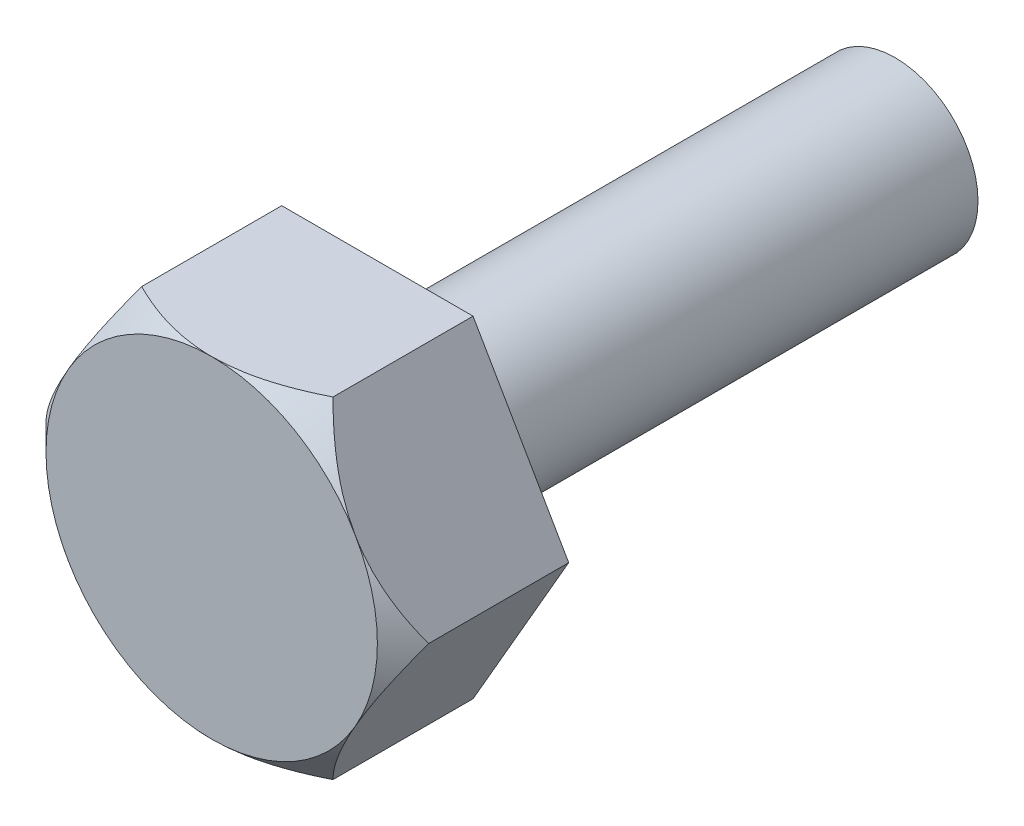
SolidWorks part; units mm, degrees
ref_plane "Front Plane" through (0, 0, 0) normal (0, 0, 1) x (1, 0, 0)
ref_plane "Top Plane" through (0, 0, 0) normal (0, 1, 0) x (1, 0, 0)
ref_plane "Right Plane" through (0, 0, 0) normal (1, 0, 0) x (0, 0, -1)
sketch "Sketch1" plane through (0, 0, 0) normal (0, 0, 1) x (1, 0, 0)
  line L1 (9.2376, 0) -> (4.6188, 8)
  line L2 (4.6188, 8) -> (-4.6188, 8)
  line L3 (-4.6188, 8) -> (-9.2376, 0)
  line L4 (-9.2376, 0) -> (-4.6188, -8)
  line L5 (-4.6188, -8) -> (4.6188, -8)
  line L6 (4.6188, -8) -> (9.2376, 0)
  circle A0 centre (0, 0) radius 8 construction
  dimension "D1" = 16
extrude "Boss-Extrude1" add sketch "Sketch1" along normal blind 8
sketch "Sketch2" plane through (0, 0, 8) normal (0, 0, 1) x (1, 0, 0)
  circle A0 centre (0, 0) radius 8
extrude "Cut-Extrude1" cut sketch "Sketch2" against normal blind 8 draft 45 flip side to cut
sketch "Sketch3" plane through (0, 0, 0) normal (0, 0, -1) x (-1, 0, 0)
  circle A0 centre (0, 0) radius 4
  dimension "D1" = 8
extrude "Boss-Extrude2" add sketch "Sketch3" along normal blind 25
